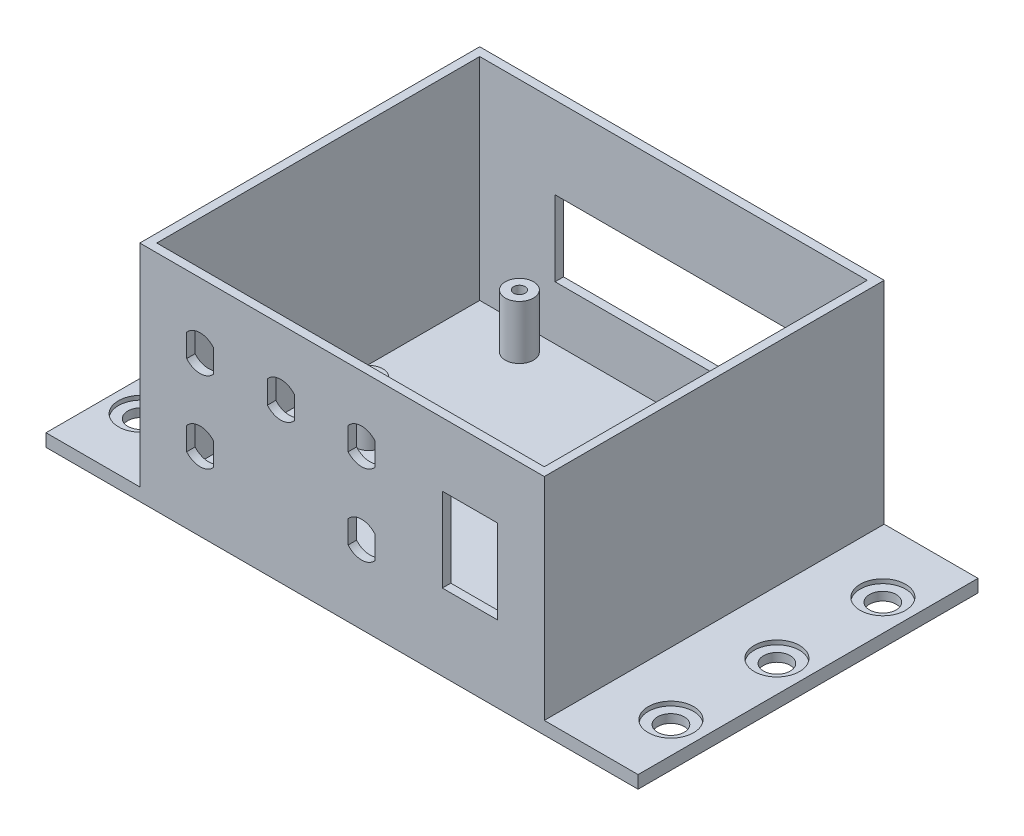
SolidWorks part; units mm, degrees
ref_plane "Front Plane" through (0, 0, 0) normal (0, 0, 1) x (1, 0, 0)
ref_plane "Top Plane" through (0, 0, 0) normal (0, 1, 0) x (1, 0, 0)
ref_plane "Right Plane" through (0, 0, 0) normal (1, 0, 0) x (0, 0, -1)
sketch "Sketch1" plane through (0, 0, 0) normal (0, 1, 0) x (1, 0, 0)
  line L1 (-26.416, 22.9716) -> (39.624, 22.9716) construction
  line L2 (-26.416, 22.9716) -> (-26.416, -17.6684) construction
  line L3 (-26.416, -17.6684) -> (39.624, -17.6684) construction
  line L4 (39.624, 22.9716) -> (39.624, -17.6684) construction
  line L5 (-43.4106, 25.1434) -> (48.0294, 25.1434)
  line L6 (-43.4106, 25.1434) -> (-43.4106, -51.0566)
  line L7 (-43.4106, -51.0566) -> (48.0294, -51.0566)
  line L8 (48.0294, 25.1434) -> (48.0294, -51.0566)
  line L9 (-23.8578, -32.0066) -> (-15.2211, -32.0066) construction
  line L10 (-23.8578, -32.0066) -> (-23.8578, -51.0566) construction
  line L11 (-23.8578, -51.0566) -> (-15.2211, -51.0566)
  line L12 (-15.2211, -32.0066) -> (-15.2211, -51.0566) construction
  line L13 (-45.4106, 27.1434) -> (50.0294, 27.1434)
  line L14 (-45.4106, 27.1434) -> (-45.4106, -53.0566)
  line L15 (-45.4106, -53.0566) -> (50.0294, -53.0566)
  line L16 (50.0294, 27.1434) -> (50.0294, -53.0566)
  dimension "D1" = 66.04
  dimension "D2" = 40.64
  dimension "D3" = 91.44
  dimension "D4" = 76.2
  dimension "D5" = 19.05
  dimension "D6" = 2
  dimension "D7" = 2
  dimension "D8" = 2
  dimension "D9" = 2
extrude "Boss-Extrude1" add sketch "Sketch1" along normal blind 52.832 contours L16 L13 L14 L15 L5 L8 L7 L6
sketch "Sketch2" plane through (0, 0, 0) normal (0, 1, 0) x (1, 0, 0)
  line L0 (50.0294, -12.9566) -> (64.8094, -12.9566) construction
  line L1 (-67.5406, 27.1434) -> (72.1594, 27.1434)
  line L2 (-67.5406, 27.1434) -> (-67.5406, -53.0566)
  line L3 (-67.5406, -53.0566) -> (72.1594, -53.0566)
  line L4 (72.1594, 27.1434) -> (72.1594, -53.0566)
  line L5 (-60.1906, 12.0434) -> (64.8094, 12.0434) construction
  line L6 (-60.1906, 12.0434) -> (-60.1906, -37.9566) construction
  line L7 (-60.1906, -37.9566) -> (64.8094, -37.9566) construction
  line L8 (64.8094, 12.0434) -> (64.8094, -37.9566) construction
  line L9 (50.0294, 27.1434) -> (50.0294, -53.0566) construction
  line L10 (2.3094, 25.1434) -> (2.3094, 12.0434) construction
  line L11 (-43.4106, 25.1434) -> (48.0294, 25.1434) construction
  line L12 (-45.4106, -53.0566) -> (50.0294, -53.0566) construction
  line L14 (-45.4106, -12.9566) -> (-67.5406, -12.9566) construction
  line L15 (-45.4106, 27.1434) -> (-45.4106, -53.0566) construction
  circle A0 centre (-60.1906, 12.0434) radius 3.15
  circle A1 centre (64.8094, 12.0434) radius 3.15
  circle A2 centre (-60.1906, -37.9566) radius 3.15
  circle A3 centre (64.8094, -37.9566) radius 3.15
  circle A4 centre (-60.1906, -12.9566) radius 3.15
  circle A5 centre (64.8094, -12.9566) radius 3.15
  dimension "D1" = 6.3
  dimension "D2" = 50
  dimension "D3" = 125
  dimension "D5" = 139.7
extrude "Boss-Extrude2" add sketch "Sketch2" along normal blind 3
sketch "Sketch3" plane through (0, 3, 0) normal (0, 1, 0) x (1, 0, 0)
  circle A0 centre (-60.1906, 12.0434) radius 5.35
  circle A1 centre (-60.1906, -12.9566) radius 5.35
  circle A2 centre (-60.1906, -37.9566) radius 5.35
  circle A3 centre (64.8094, 12.0434) radius 5.35
  circle A4 centre (64.8094, -12.9566) radius 5.35
  circle A5 centre (64.8094, -37.9566) radius 5.35
  dimension "D1" = 10.7
extrude "Cut-Extrude1" cut sketch "Sketch3" against normal blind 1
sketch "Sketch4" plane through (0, 3, 0) normal (0, 1, 0) x (1, 0, 0)
  line L0 (2.3094, 25.1434) -> (2.3094, 19.276) construction
  line L1 (-28.1706, 19.276) -> (32.7894, 19.276) construction
  line L2 (-28.1706, 19.276) -> (-28.1706, -16.284) construction
  line L3 (-28.1706, -16.284) -> (32.7894, -16.284) construction
  line L4 (32.7894, 19.276) -> (32.7894, -16.284) construction
  line L5 (-43.4106, 25.1434) -> (48.0294, 25.1434) construction
  line L6 (-28.1706, 22.6034) -> (-28.1706, 25.1434) construction
  circle A0 centre (-28.1706, 19.276) radius 3.3274
  circle A1 centre (32.7894, 19.276) radius 3.3274
  circle A2 centre (32.7894, -16.284) radius 3.3274
  circle A3 centre (-28.1706, -16.284) radius 3.3274
  circle A4 centre (-28.1706, -16.284) radius 1.3589
  circle A5 centre (-28.1706, 19.276) radius 1.3589
  circle A6 centre (32.7894, 19.276) radius 1.3589
  circle A7 centre (32.7894, -16.284) radius 1.3589
  dimension "D3" = 6.6548
  dimension "D4" = 2.7178
  dimension "D1" = 60.96
  dimension "D2" = 35.56
  dimension "D5" = 2.54
extrude "Boss-Extrude3" add sketch "Sketch4" along normal blind 12.7
sketch "Sketch5" plane through (0, 0, -27.1434) normal (0, 0, -1) x (-1, 0, 0)
  line L0 (-50.0294, 3) -> (45.4106, 3) construction
  line L1 (-30.2494, 33.48) -> (25.6306, 33.48)
  line L2 (-30.2494, 33.48) -> (-30.2494, 15.7)
  line L3 (-30.2494, 15.7) -> (25.6306, 15.7)
  line L4 (25.6306, 33.48) -> (25.6306, 15.7)
  line L7 (-2.3094, 3) -> (-2.3094, 15.7) construction
  dimension "D1" = 17.78
  dimension "D2" = 55.88
  dimension "D3" = 12.7
extrude "Cut-Extrude2" cut sketch "Sketch5" against normal up to next
sketch "Sketch6" plane through (0, 0, 53.0566) normal (0, 0, 1) x (1, 0, 0)
  line L0 (-45.4106, 3) -> (50.0294, 3) construction
  line L1 (-31.1781, 33.2754) -> (-31.1781, 41.6066) construction
  line L2 (-31.1781, 33.2754) -> (-31.1781, 34.0182) construction
  line L3 (-34.3531, 40.1376) -> (-34.3531, 34.7444)
  line L4 (-34.3531, 34.0182) -> (-28.0031, 34.0182) construction
  line L5 (-28.0031, 40.1376) -> (-28.0031, 34.7444)
  line L6 (-34.3531, 34.7444) -> (-34.3531, 34.0182) construction
  line L7 (-28.0031, 34.0182) -> (-28.0031, 34.7444) construction
  line L8 (-12.1281, 33.2754) -> (-12.1281, 41.6066) construction
  line L9 (-12.1281, 33.2754) -> (-12.1281, 34.2983) construction
  line L10 (-15.3031, 40.1376) -> (-15.3031, 34.7444)
  line L11 (-15.3031, 34.2983) -> (-8.9531, 34.2983) construction
  line L12 (-8.9531, 40.1376) -> (-8.9531, 34.7444)
  line L13 (-15.3031, 34.7444) -> (-15.3031, 34.2983) construction
  line L14 (-8.9531, 34.2983) -> (-8.9531, 34.7444) construction
  line L15 (6.9219, 33.2754) -> (6.9219, 41.6066) construction
  line L16 (6.9219, 33.2754) -> (6.9219, 34.3123) construction
  line L17 (3.7469, 40.1376) -> (3.7469, 34.7444)
  line L18 (3.7469, 34.3123) -> (10.0969, 34.3123) construction
  line L19 (10.0969, 40.1376) -> (10.0969, 34.7444)
  line L20 (3.7469, 34.7444) -> (3.7469, 34.3123) construction
  line L21 (10.0969, 34.3123) -> (10.0969, 34.7444) construction
  line L22 (-31.1781, 14.2254) -> (-31.1781, 22.5566) construction
  line L23 (-31.1781, 14.2254) -> (-31.1781, 15.0798) construction
  line L24 (-34.3531, 21.0876) -> (-34.3531, 15.6944)
  line L25 (-34.3531, 15.0798) -> (-28.0031, 15.0798) construction
  line L26 (-28.0031, 21.0876) -> (-28.0031, 15.6944)
  line L27 (-34.3531, 15.6944) -> (-34.3531, 15.0798) construction
  line L28 (-28.0031, 15.0798) -> (-28.0031, 15.6944) construction
  line L29 (6.9219, 14.2254) -> (6.9219, 22.5566) construction
  line L30 (6.9219, 14.2254) -> (6.9219, 17.2109) construction
  line L31 (3.7469, 21.0876) -> (3.7469, 15.6944)
  line L32 (3.7469, 17.2109) -> (10.0969, 17.2109) construction
  line L33 (10.0969, 21.0876) -> (10.0969, 15.6944)
  line L34 (3.7469, 15.6944) -> (3.7469, 17.2109) construction
  line L35 (10.0969, 17.2109) -> (10.0969, 15.6944) construction
  line L36 (-45.4106, 52.832) -> (-45.4106, 3) construction
  line L37 (-31.1781, 37.441) -> (6.9219, 37.441) construction
  line L38 (-31.1781, 37.441) -> (-31.1781, 18.391) construction
  line L39 (-31.1781, 18.391) -> (6.9219, 18.391) construction
  line L40 (6.9219, 37.441) -> (6.9219, 18.391) construction
  line L41 (-34.3531, 34.7444) -> (-34.3531, 21.0876) construction
  line L42 (38.9719, 27.916) -> (50.0294, 27.916) construction
  line L43 (25.9719, 37.816) -> (38.9719, 37.816)
  line L44 (25.9719, 37.816) -> (25.9719, 18.016)
  line L45 (25.9719, 18.016) -> (38.9719, 18.016)
  line L46 (38.9719, 37.816) -> (38.9719, 18.016)
  line L47 (50.0294, 52.832) -> (50.0294, 3) construction
  line L48 (6.9219, 27.916) -> (25.9719, 27.916) construction
  line L49 (-45.4106, 27.916) -> (-34.3531, 27.916) construction
  arc A0 (-28.0031, 40.1376) -> (-34.3531, 40.1376) centre (-31.1781, 37.441) ccw
  arc A1 (-34.3531, 34.7444) -> (-28.0031, 34.7444) centre (-31.1781, 37.441) ccw
  arc A2 (-8.9531, 40.1376) -> (-15.3031, 40.1376) centre (-12.1281, 37.441) ccw
  arc A3 (-15.3031, 34.7444) -> (-8.9531, 34.7444) centre (-12.1281, 37.441) ccw
  arc A4 (10.0969, 40.1376) -> (3.7469, 40.1376) centre (6.9219, 37.441) ccw
  arc A5 (3.7469, 34.7444) -> (10.0969, 34.7444) centre (6.9219, 37.441) ccw
  arc A6 (-28.0031, 21.0876) -> (-34.3531, 21.0876) centre (-31.1781, 18.391) ccw
  arc A7 (-34.3531, 15.6944) -> (-28.0031, 15.6944) centre (-31.1781, 18.391) ccw
  arc A8 (10.0969, 21.0876) -> (3.7469, 21.0876) centre (6.9219, 18.391) ccw
  arc A9 (3.7469, 15.6944) -> (10.0969, 15.6944) centre (6.9219, 18.391) ccw
  point P24 (-12.1281, 37.441)
  point P34 (-45.4106, 27.916)
  point P54 (-31.1781, 27.916)
  dimension "D2" = 8.3312
  dimension "D1" = 6.35
  dimension "D3" = 19.05
  dimension "D4" = 19.05
  dimension "D6" = 13
  dimension "D7" = 19.8
  dimension "D8" = 19.05
extrude "Cut-Extrude3" cut sketch "Sketch6" against normal up to next
